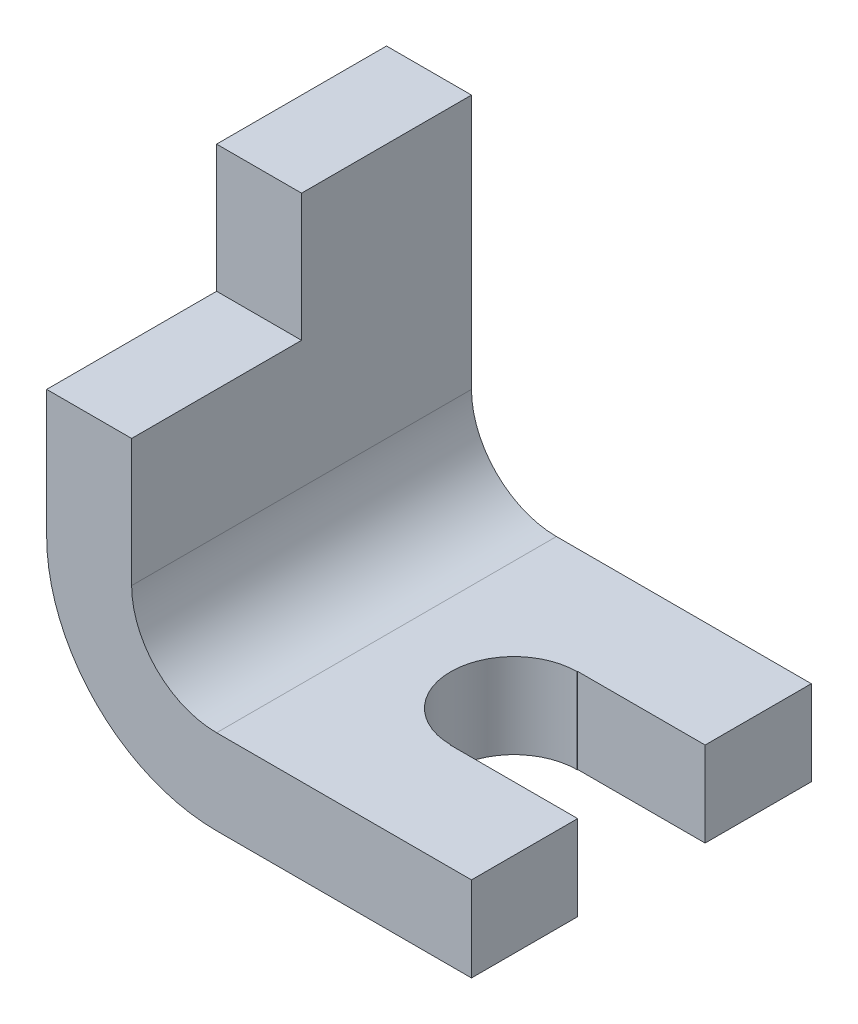
SolidWorks part; units mm, degrees
ref_plane "Front Plane" through (0, 0, 0) normal (0, 0, 1) x (1, 0, 0)
ref_plane "Top Plane" through (0, 0, 0) normal (0, 1, 0) x (1, 0, 0)
ref_plane "Right Plane" through (0, 0, 0) normal (1, 0, 0) x (0, 0, -1)
sketch "Sketch1" plane through (0, 0, 0) normal (0, 0, 1) x (1, 0, 0)
  line L0 (20, 0) -> (50, 0)
  line L1 (0, 20) -> (0, 50)
  line L2 (0, 50) -> (10, 50)
  line L3 (10, 50) -> (10, 20)
  line L4 (20, 10) -> (50, 10)
  line L5 (50, 10) -> (50, 0)
  arc A0 (20, 10) -> (10, 20) centre (20, 20) cw
  arc A1 (20, 0) -> (0, 20) centre (20, 20) cw
  point P11 (0, 0)
  dimension "D5" = 10
  dimension "D6" = 20
  dimension "D1" = 50
  dimension "D2" = 50
  dimension "D3" = 10
  dimension "D4" = 10
extrude "Boss-Extrude1" add sketch "Sketch1" against normal blind 40
sketch "Sketch3" plane through (10, 0, 0) normal (1, 0, 0) x (0, 0, -1)
  line L1 (0, 50) -> (20, 50)
  line L2 (0, 50) -> (0, 35)
  line L3 (0, 35) -> (20, 35)
  line L4 (20, 50) -> (20, 35)
  dimension "D1" = 15
  dimension "D2" = 20
extrude "Cut-Extrude1" cut sketch "Sketch3" against normal blind 10
sketch "Sketch4" plane through (0, 10, 0) normal (0, 1, 0) x (1, 0, 0)
  line L0 (35, 12.5) -> (50, 12.5)
  line L1 (35, 27.5) -> (50, 27.5)
  line L2 (35, 12.5) -> (35, 12.5511)
  line L3 (50, 40) -> (50, 0) construction
  line L4 (50, 0) -> (20, 0) construction
  line L5 (35, 27.4489) -> (35, 27.5)
  arc A0 (35, 27.4489) -> (35, 12.5511) centre (35, 20) ccw
  dimension "D1" = 15
  dimension "D2" = 15
  dimension "D3" = 12.5
extrude "Cut-Extrude5" cut sketch "Sketch4" against normal blind 10 and the other way through all flip side to cut
